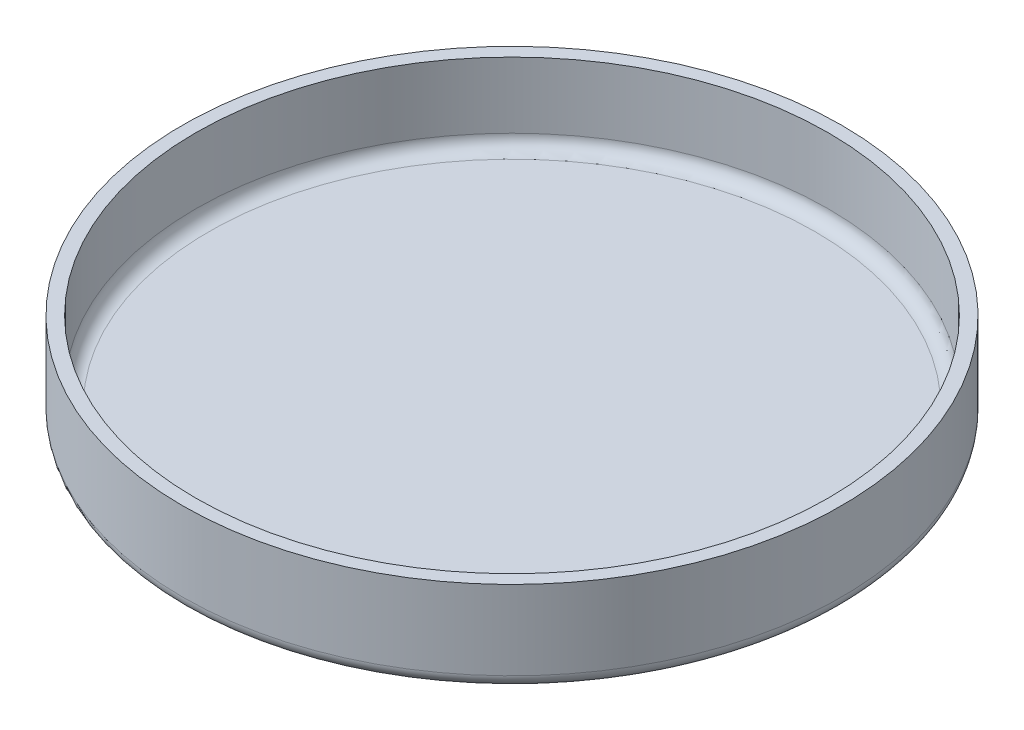
SolidWorks part; units mm, degrees
material "1060 Alloy"
ref_plane "Front Plane" through (0, 0, 0) normal (0, 0, 1) x (1, 0, 0)
ref_plane "Top Plane" through (0, 0, 0) normal (0, 1, 0) x (1, 0, 0)
ref_plane "Right Plane" through (0, 0, 0) normal (1, 0, 0) x (0, 0, -1)
sketch "Sketch1" plane through (0, 0, 0) normal (0, 1, 0) x (1, 0, 0)
  circle A0 centre (0, 0) radius 25
  dimension "D1" = 50
extrude "Boss-Extrude1" add sketch "Sketch1" along normal blind 7
sketch "Sketch2" plane through (0, 7, 0) normal (0, 1, 0) x (1, 0, 0)
  circle A0 centre (0, 0) radius 24
  dimension "D1" = 48
extrude "Cut-Extrude1" cut sketch "Sketch2" against normal blind 6
fillet "Fillet1" radius 1 2 edges at (0, 0, 25) (0, 1, 24)
